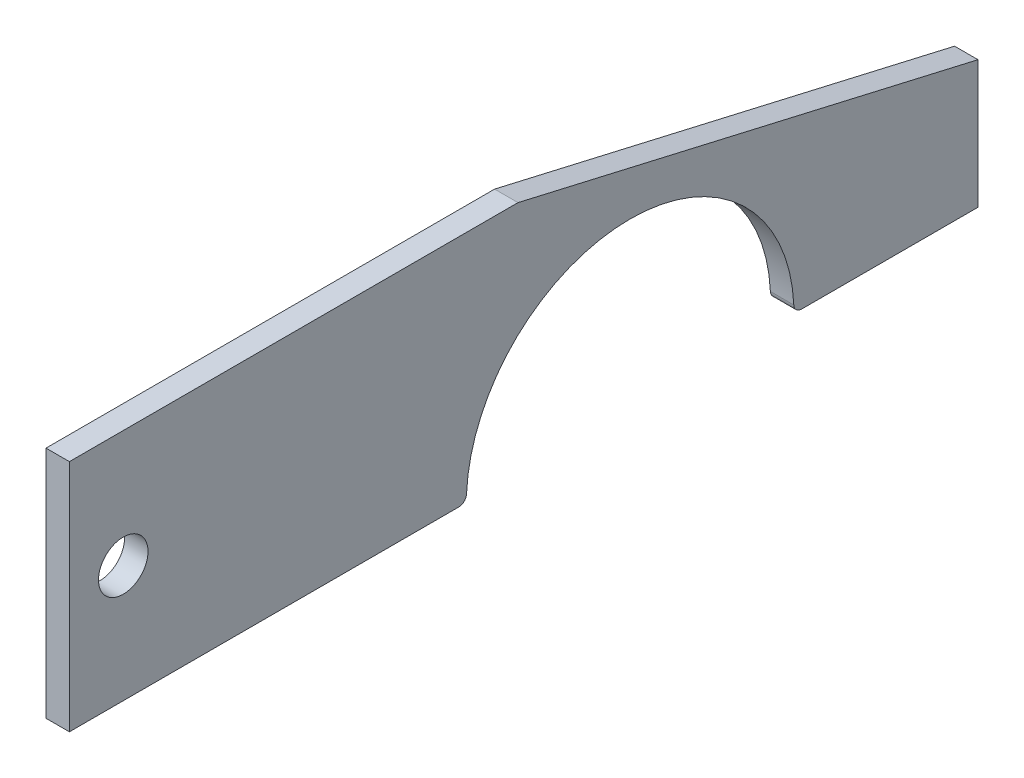
SolidWorks part; units mm, degrees
ref_plane "Front Plane" through (0, 0, 0) normal (0, 0, 1) x (1, 0, 0)
ref_plane "Top Plane" through (0, 0, 0) normal (0, 1, 0) x (1, 0, 0)
ref_plane "Right Plane" through (0, 0, 0) normal (1, 0, 0) x (0, 0, -1)
sketch "Sketch1" plane through (0, 0, 0) normal (1, 0, 0) x (0, 0, -1)
  line L0 (0, 0) -> (57.5041, 0)
  line L3 (50.8832, -30) -> (0, -30)
  line L4 (0, -30) -> (0, 0)
  line L6 (116.4748, -30) -> (92.8832, -30)
  line L7 (92.8832, -30) -> (50.8832, -30) construction
  line L8 (116.4748, -30) -> (116.4748, -13.6151)
  line L9 (116.4748, -13.6151) -> (57.5041, 0)
  arc A0 (50.8832, -30) -> (92.8832, -30) centre (71.8832, -30) cw
  dimension "D3" = 21
  dimension "D1" = 30
extrude "Boss-Extrude1" add sketch "Sketch1" along normal blind 3
sketch "Sketch2" plane through (3, 0, 0) normal (1, 0, 0) x (0, 0, -1)
  line L0 (0, 0) -> (0, -30) construction
  circle A0 centre (6.9009, -15) radius 3.175
  point P4 (0, -15)
  dimension "D1" = 6.35
extrude "Cut-Extrude1" cut sketch "Sketch2" against normal through all
fillet "Fillet2" radius 1 2 edges at (1.5, -30, -50.8832) (1.5, -30, -92.8832)
